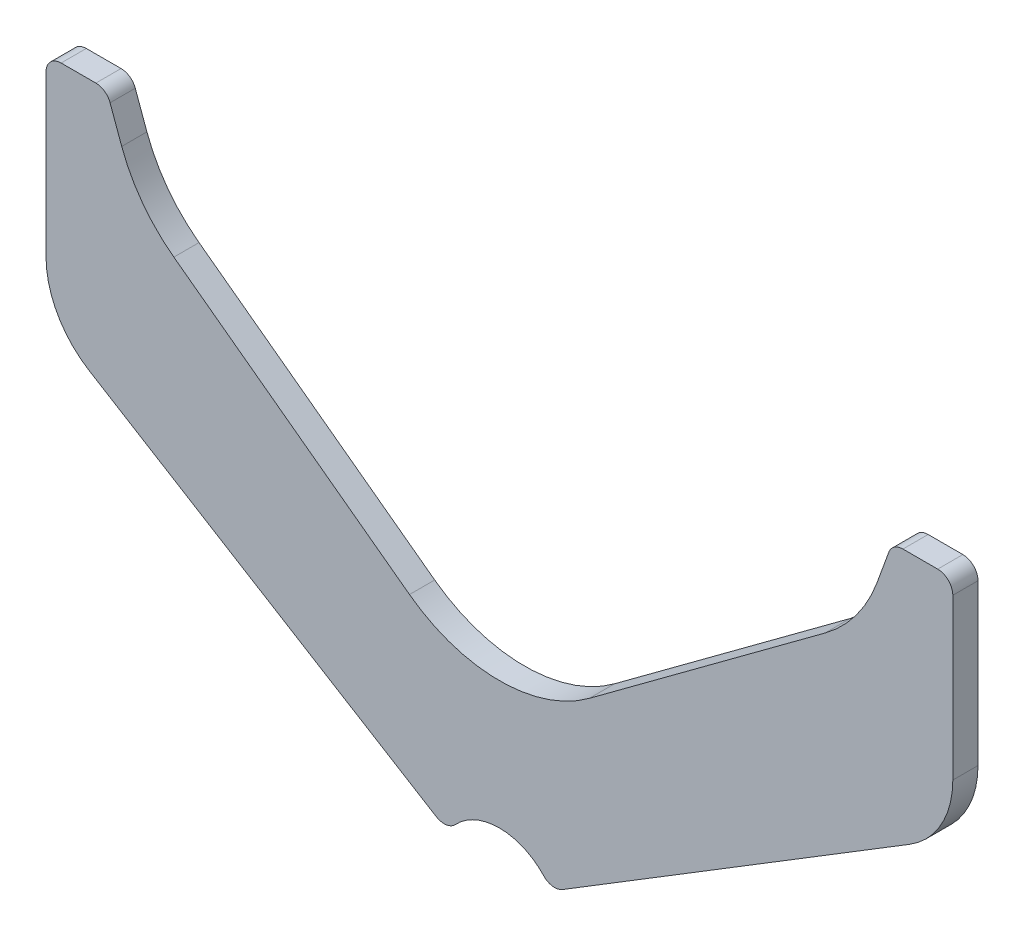
SolidWorks part; units mm, degrees
ref_plane "Plane1" through (0, 0, 0) normal (0, 0, 1) x (1, 0, 0)
ref_plane "Plane2" through (0, 0, 0) normal (0, 1, 0) x (1, 0, 0)
ref_plane "Plane3" through (0, 0, 0) normal (1, 0, 0) x (0, 0, -1)
sketch "Sketch1" plane through (0, 0, 0) normal (0, 0, 1) x (1, 0, 0)
  line L2 (-90, 97) -> (-90, 65.2326)
  line L3 (-81.405, 49.885) -> (-12.5312, 7.6791)
  line L4 (0, 200) -> (0, 0) construction
  line L6 (17.8447, 43.2044) -> (64.6235, 77.8189)
  line L7 (-17.8447, 43.2044) -> (-64.6235, 77.8189)
  line L10 (-74.9696, 91.674) -> (-77.2815, 98.0261)
  line L11 (-80.1006, 100) -> (-87, 100)
  line L13 (80.1006, 100) -> (87, 100)
  line L14 (74.9696, 91.674) -> (77.2815, 98.0261)
  line L16 (81.405, 49.885) -> (12.5312, 7.6791)
  line L17 (90, 97) -> (90, 65.2326)
  arc A0 (8.771, 8.1896) -> (-8.771, 8.1896) centre (0, 0) ccw
  arc A1 (12.5312, 7.6791) -> (8.771, 8.1896) centre (10.9637, 10.237) cw
  arc A2 (-12.5312, 7.6791) -> (-8.771, 8.1896) centre (-10.9637, 10.237) ccw
  arc A3 (17.8447, 43.2044) -> (-17.8447, 43.2044) centre (0, 67.3201) cw
  arc A6 (-80.1006, 100) -> (-77.2815, 98.0261) centre (-80.1006, 97) cw
  arc A7 (-90, 97) -> (-87, 100) centre (-87, 97) cw
  arc A8 (77.2815, 98.0261) -> (80.1006, 100) centre (80.1006, 97) cw
  arc A9 (90, 97) -> (87, 100) centre (87, 97) ccw
  arc A10 (-81.405, 49.885) -> (-90, 65.2326) centre (-72, 65.2326) cw
  arc A11 (90, 65.2326) -> (81.405, 49.885) centre (72, 65.2326) cw
  arc A13 (64.6235, 77.8189) -> (74.9696, 91.674) centre (46.7788, 101.9346) ccw
  arc A14 (-74.9696, 91.674) -> (-64.6235, 77.8189) centre (-46.7788, 101.9346) ccw
  point P3 (-78, 100)
  point P7 (0, 30)
  point P16 (-90, 100)
  point P34 (78, 100)
  point P37 (90, 100)
  point P40 (-90, 55.1521)
  point P43 (90, 55.1521)
  dimension "D8" = 30
  dimension "D12" = 3
  dimension "D13" = 18
  dimension "D14" = 30
  dimension "D6" = 12
  dimension "D7" = 3
  dimension "D2" = 30
  dimension "D3" = 20
  dimension "D4" = 12
  dimension "D5" = 100
  dimension "D10" = 180
  dimension "D11" = 63
  dimension "D18" = 5
extrude "Base-Extrude" add sketch "Sketch1" along normal blind 5
